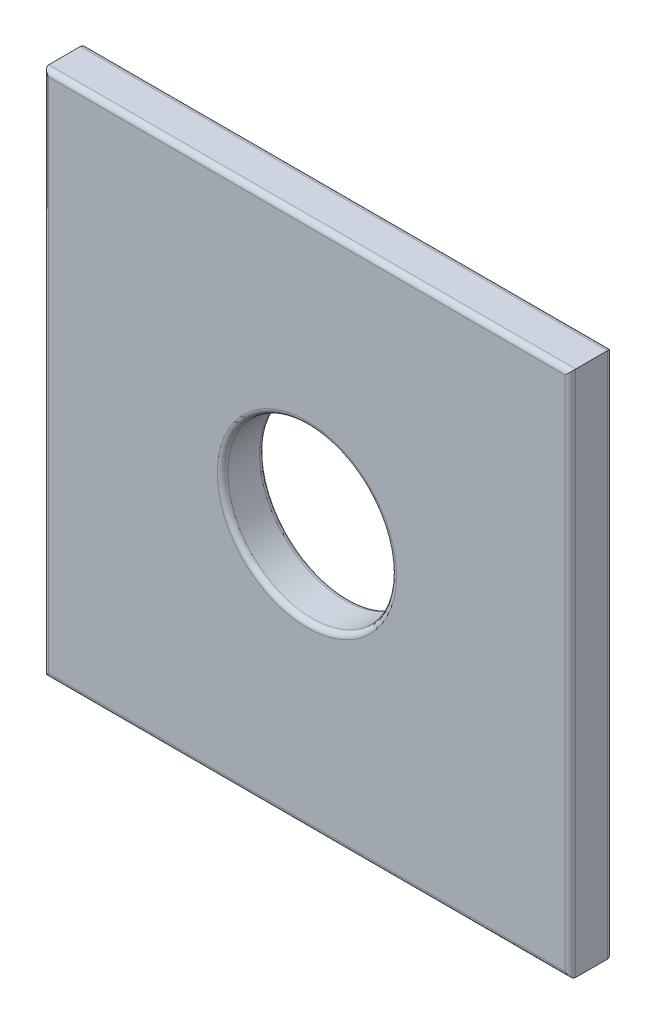
SolidWorks part; units mm, degrees
ref_plane "Płaszczyzna przednia" through (0, 0, 0) normal (0, 0, 1) x (1, 0, 0)
ref_plane "Płaszczyzna górna" through (0, 0, 0) normal (0, 1, 0) x (1, 0, 0)
ref_plane "Płaszczyzna prawa" through (0, 0, 0) normal (1, 0, 0) x (0, 0, -1)
sketch "Szkic1" plane through (0, 0, 0) normal (0, 0, 1) x (1, 0, 0)
  line L0 (-1005.5558, -150.5822) -> (-1055.5558, -150.5822) construction
  line L1 (-1005.5558, -125.5822) -> (-1055.5558, -125.5822)
  line L2 (-1005.5558, -125.5822) -> (-1005.5558, -175.5822)
  line L3 (-1005.5558, -175.5822) -> (-1055.5558, -175.5822)
  line L4 (-1055.5558, -125.5822) -> (-1055.5558, -175.5822)
  circle A0 centre (-1030.5558, -150.5822) radius 8
  point P6 (-1038.9403, -155.4706)
  point P9 (-1030.5558, -150.5822)
  point P10 (0, 0)
  point P11 (-1055.5558, -150.5822)
  point P12 (-1055.5558, -125.5822)
  point P13 (0, 0)
  point P14 (-1005.5558, -150.5822)
  dimension "D3" = 16
  dimension "D1" = 50
  dimension "D2" = 50
extrude "Dodanie-wyciągnięcie1" add sketch "Szkic1" along normal blind 4 contours L2 L0 A0 L4 L3 | L0 L2 L1 L4 A0
fillet "Zaokrąglenie1" radius 0.5 10 edges at (-1030.5558, -125.5822, 0) (-1055.5558, -150.5822, 0) (-1030.5558, -175.5822, 0) (-1005.5558, -150.5822, 0) (-1022.5558, -150.5822, 0) (-1030.5558, -175.5822, 4) (-1055.5558, -150.5822, 4) (-1030.5558, -125.5822, 4) (-1005.5558, -150.5822, 4) (-1022.5558, -150.5822, 4)
